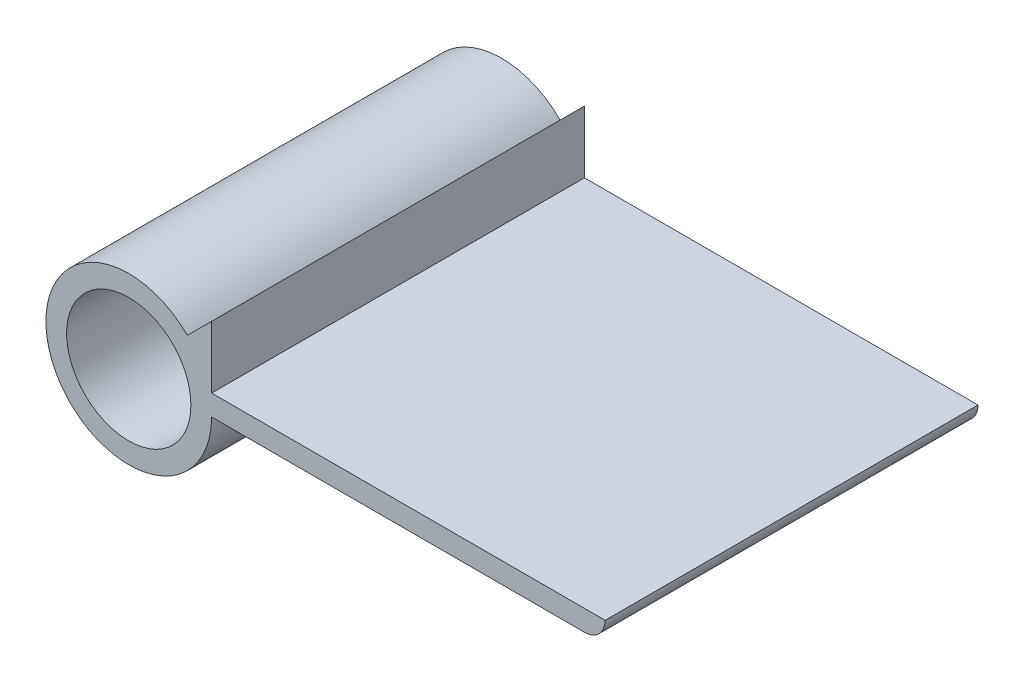
SolidWorks part; units mm, degrees
ref_plane "Front Plane" through (0, 0, 0) normal (0, 0, 1) x (1, 0, 0)
ref_plane "Top Plane" through (0, 0, 0) normal (0, 1, 0) x (1, 0, 0)
ref_plane "Right Plane" through (0, 0, 0) normal (1, 0, 0) x (0, 0, -1)
sketch "Sketch2" plane through (0, 0, 0) normal (0, 0, 1) x (1, 0, 0)
  line L2 (46, 2) -> (8, 2)
  line L4 (8, 2) -> (8, 8)
  line L5 (8, 0) -> (44, 0)
  line L6 (8, 8) -> (5.6569, 5.6569)
  line L7 (0, 8) -> (17.1054, 8) construction
  line L8 (0, 0) -> (0, 2) construction
  circle A0 centre (0, 0) radius 6
  arc A1 (5.6569, 5.6569) -> (8, 0) centre (0, 0) ccw
  arc A4 (46, 2) -> (44, 0) centre (44, 2) cw
  dimension "D2" = 16
  dimension "D3" = 2
  dimension "D4" = 38
  dimension "D1" = 2
  dimension "D5" = 36
  dimension "D6" = 45
extrude "Boss-Extrude2" add sketch "Sketch2" along normal blind 36
